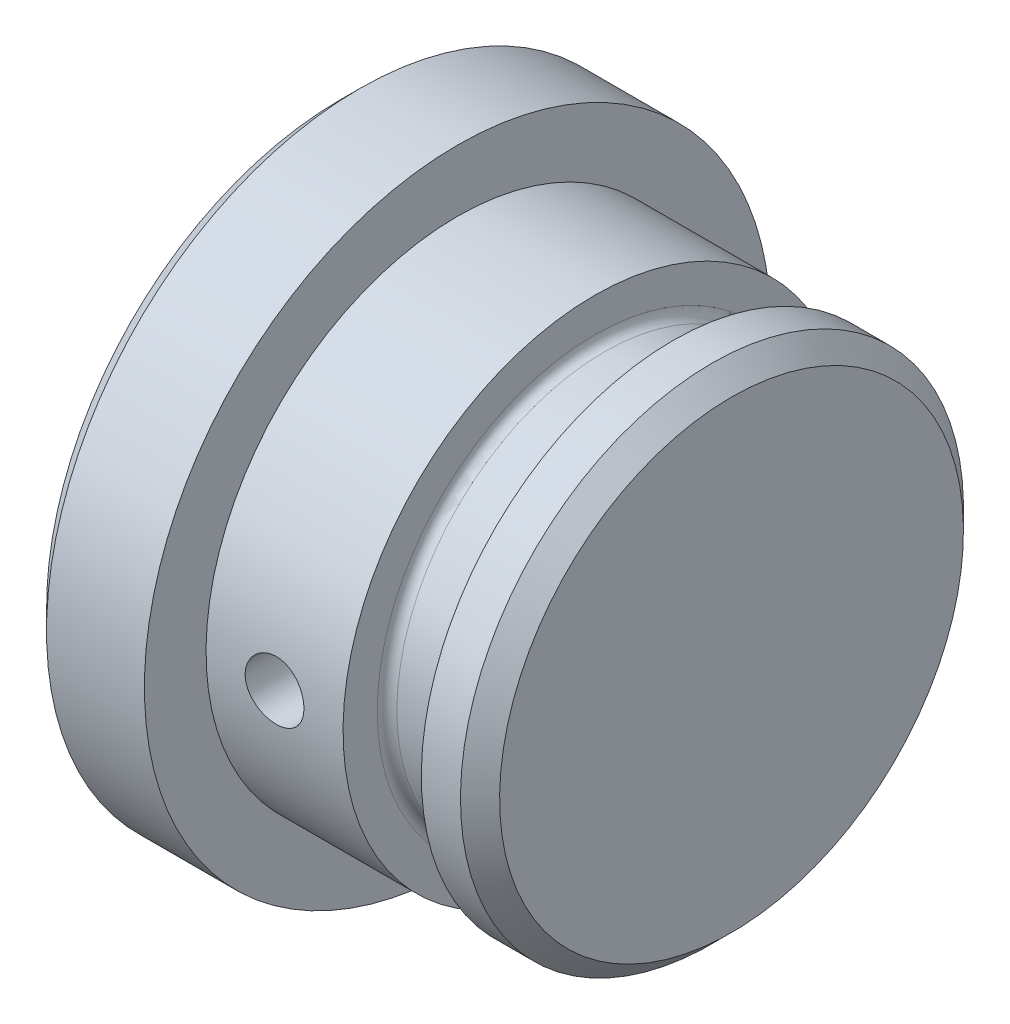
SolidWorks part; units mm, degrees
ref_plane "Plan de face" through (0, 0, 0) normal (0, 0, 1) x (1, 0, 0)
ref_plane "Plan de dessus" through (0, 0, 0) normal (0, 1, 0) x (1, 0, 0)
ref_plane "Plan de droite" through (0, 0, 0) normal (1, 0, 0) x (0, 0, -1)
sketch "Esquisse1" plane through (0, 0, 0) normal (0, 0, 1) x (1, 0, 0)
  line L0 (-170, 19.5) -> (-175, 19.5)
  line L1 (-175, 19.5) -> (-176, 18.5)
  line L2 (-176, 18.5) -> (-176, 3.5)
  line L3 (-170, 3.5) -> (-205.7, 3.5) construction
  line L4 (-170, 19.5) -> (-170, -12.5) construction
  line L5 (-170, 19.5) -> (-170, 16.35)
  line L6 (-170, 16.35) -> (-163, 16.35)
  line L7 (-157, 16.35) -> (-156, 15.35)
  line L8 (-156, 15.35) -> (-156, 3.5)
  line L9 (-156, 3.5) -> (-176, 3.5)
  line L10 (-163, 16.35) -> (-163, 14.6)
  line L11 (-162.5, 14.1) -> (-159.5, 14.1)
  line L12 (-159, 14.6) -> (-159, 16.35)
  line L13 (-159, 16.35) -> (-157, 16.35)
  arc A0 (-159, 14.6) -> (-159.5, 14.1) centre (-159.5, 14.6) cw
  arc A1 (-162.5, 14.1) -> (-163, 14.6) centre (-162.5, 14.6) cw
  dimension "D7" = 0.5
  dimension "D1" = 25.7
  dimension "D2" = 1
  dimension "D3" = 1
  dimension "D4" = 1
  dimension "D5" = 1
  dimension "D6" = 6
  dimension "D8" = 4
  dimension "D9" = 2.25
  dimension "D10" = 3
  dimension "D11" = 14
revolve "Révolution1" add sketch "Esquisse1" angle 360 about L3
sketch "Esquisse2" plane through (0, 0, 0) normal (0, 0, 1) x (1, 0, 0)
  line L0 (-170, 3.5) -> (-163, 3.5) construction
  line L1 (-170, -12.5) -> (-170, 19.5) construction
  line L2 (-163, -9.35) -> (-163, 16.35) construction
  circle A0 centre (-166.5, 3.5) radius 1.5
  dimension "D1" = 3
extrude "Enlèv. mat.-Extru.1" cut sketch "Esquisse2" against normal through all both and the other way through all
